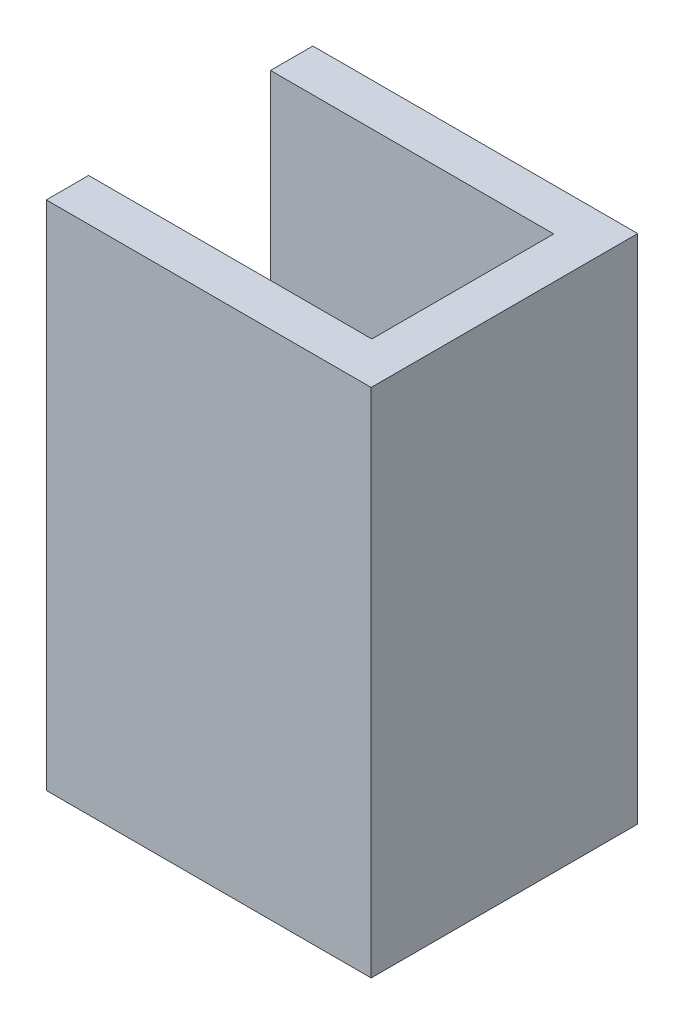
SolidWorks part; units mm, degrees
ref_plane "Front Plane" through (0, 0, 0) normal (0, 0, 1) x (1, 0, 0)
ref_plane "Top Plane" through (0, 0, 0) normal (0, 1, 0) x (1, 0, 0)
ref_plane "Right Plane" through (0, 0, 0) normal (1, 0, 0) x (0, 0, -1)
sketch "Sketch2" plane through (0, 0, 0) normal (1, 0, 0) x (0, 0, -1)
  line L1 (8, -15.35) -> (-8, -15.35)
  line L2 (8, -15.35) -> (8, 15.35)
  line L3 (8, 15.35) -> (-8, 15.35)
  line L4 (-8, -15.35) -> (-8, 15.35)
  line L5 (8, -15.35) -> (-8, 15.35) construction
  line L6 (8, 15.35) -> (-8, -15.35) construction
  point P0 (0, 0)
  dimension "D1" = 16
  dimension "D2" = 30.7
extrude "Boss-Extrude1" add sketch "Sketch2" along normal mid plane 19.5
sketch "Sketch3" plane through (-9.75, 0, 0) normal (-1, 0, 0) x (0, 0, 1)
  line L0 (-5.46, 15.35) -> (-5.46, -13.75)
  line L1 (-8, 15.35) -> (8, 15.35) construction
  line L2 (-5.46, -13.75) -> (5.46, -13.75)
  line L3 (5.46, -13.75) -> (5.46, 15.35)
  line L4 (0, 20.0385) -> (0, -21.833) construction
  line L5 (8, -15.35) -> (-8, -15.35) construction
  line L6 (-8, -15.35) -> (-8, 15.35) construction
  line L7 (8, 15.35) -> (8, -15.35) construction
  line L8 (-5.46, 15.35) -> (5.46, 15.35)
  dimension "D1" = 1.6
  dimension "D2" = 2.54
  dimension "D3" = 2.54
extrude "Cut-Extrude1" cut sketch "Sketch3" against normal blind 17
sketch "Sketch4" plane through (-9.75, 0, 0) normal (-1, 0, 0) x (0, 0, 1)
  line L0 (-5.46, -13.75) -> (5.46, -13.75) construction
  line L1 (-5.46, -13.75) -> (5.46, -13.75)
  line L2 (-5.46, -13.75) -> (-5.46, -15.35)
  line L3 (8, -15.35) -> (-8, -15.35) construction
  line L4 (-5.46, -15.35) -> (5.46, -15.35)
  line L5 (5.46, -15.35) -> (5.46, -13.75)
extrude "Cut-Extrude2" cut sketch "Sketch4" against normal blind 5.08
sketch "Sketch5" plane through (0, -15.35, 0) normal (0, -1, 0) x (1, 0, 0)
  line L0 (-4.67, 0) -> (7.21, 0) construction
  line L1 (-4.67, -5.46) -> (-4.67, 5.46) construction
  line L3 (9.75, 8) -> (9.75, -8) construction
  circle A0 centre (1.27, 0) radius 2
  dimension "D2" = 4
  dimension "D1" = 2.54
extrude "Hole for Actuator" cut sketch "Sketch5" against normal up to surface (1.6 mm away) up to face at (1.29, -13.75, 0)
